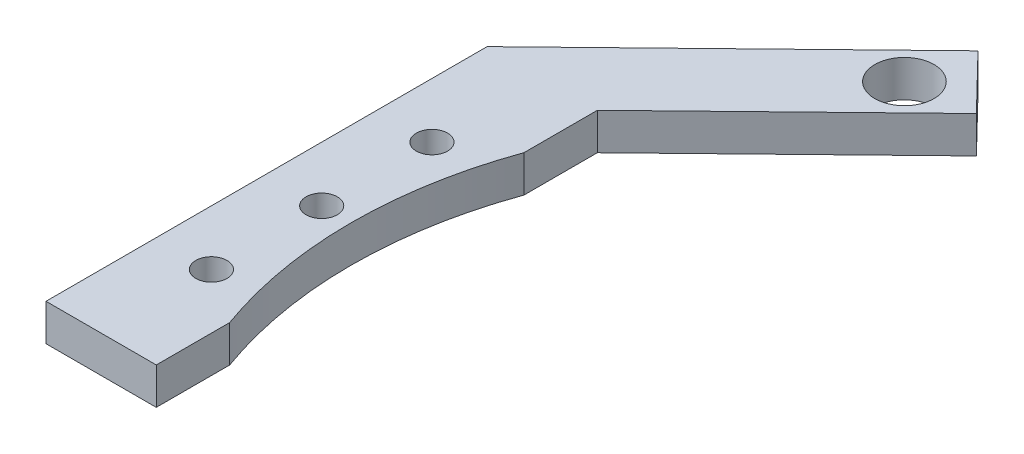
SolidWorks part; units mm, degrees
ref_plane "Front Plane" through (0, 0, 0) normal (0, 0, 1) x (1, 0, 0)
ref_plane "Top Plane" through (0, 0, 0) normal (0, 1, 0) x (1, 0, 0)
ref_plane "Right Plane" through (0, 0, 0) normal (1, 0, 0) x (0, 0, -1)
sketch "Sketch1" plane through (0, 0, 0) normal (0, 1, 0) x (1, 0, 0)
  line L0 (0, 0) -> (-63, 0) construction
  line L1 (-37.9994, 54.2688) -> (-63, 30) construction
  line L2 (0, 0) -> (-37.9994, 54.2688) construction
  line L8 (-55.5, 30) -> (-70.5, 30) construction
  line L9 (-55.5, 30) -> (-55.5, -30)
  line L13 (-55.5, -30) -> (-70.5, -30)
  line L14 (-70.5, 30) -> (-70.5, -30)
  line L15 (-63, -30) -> (-63, 30) construction
  line L16 (-55.5, 0) -> (-70.5, 0) construction
  line L17 (-70.5, 30) -> (-36.6154, 62.8929)
  line L18 (-36.6154, 62.8929) -> (-29.3381, 55.3962)
  line L19 (-29.3381, 55.3962) -> (-55.5, 30)
  circle A0 centre (0, 0) radius 55 construction
  circle A1 centre (0, 0) radius 62.5 construction
  circle A2 centre (-37.9994, 54.2688) radius 3.75 construction
  circle A5 centre (-37.9994, 54.2688) radius 4.025
  circle A7 centre (-63, 0) radius 2.125
  circle A8 centre (-63, -15) radius 2.125
  circle A9 centre (-63, 15) radius 2.125
  point P7 (-63, 0)
  dimension "D1" = 110
  dimension "D4" = 125
  dimension "D5" = 7.5
  dimension "D11" = 15
  dimension "D12" = 15
  dimension "D13" = 8.05
  dimension "D8" = 4.25
  dimension "D10" = 7
  dimension "D2" = 15
  dimension "D3" = 63
  dimension "D6" = 66.25
  dimension "D7" = 55
  dimension "D9" = 60
extrude "Boss-Extrude1" add sketch "Sketch1" along normal mid plane 5
sketch "Sketch2" plane through (0, 0, 0) normal (0, 1, 0) x (1, 0, 0)
  circle A0 centre (0, 0) radius 59
  dimension "D1" = 118
extrude "Cut-Extrude1" cut sketch "Sketch2" against normal through all both and the other way through all
